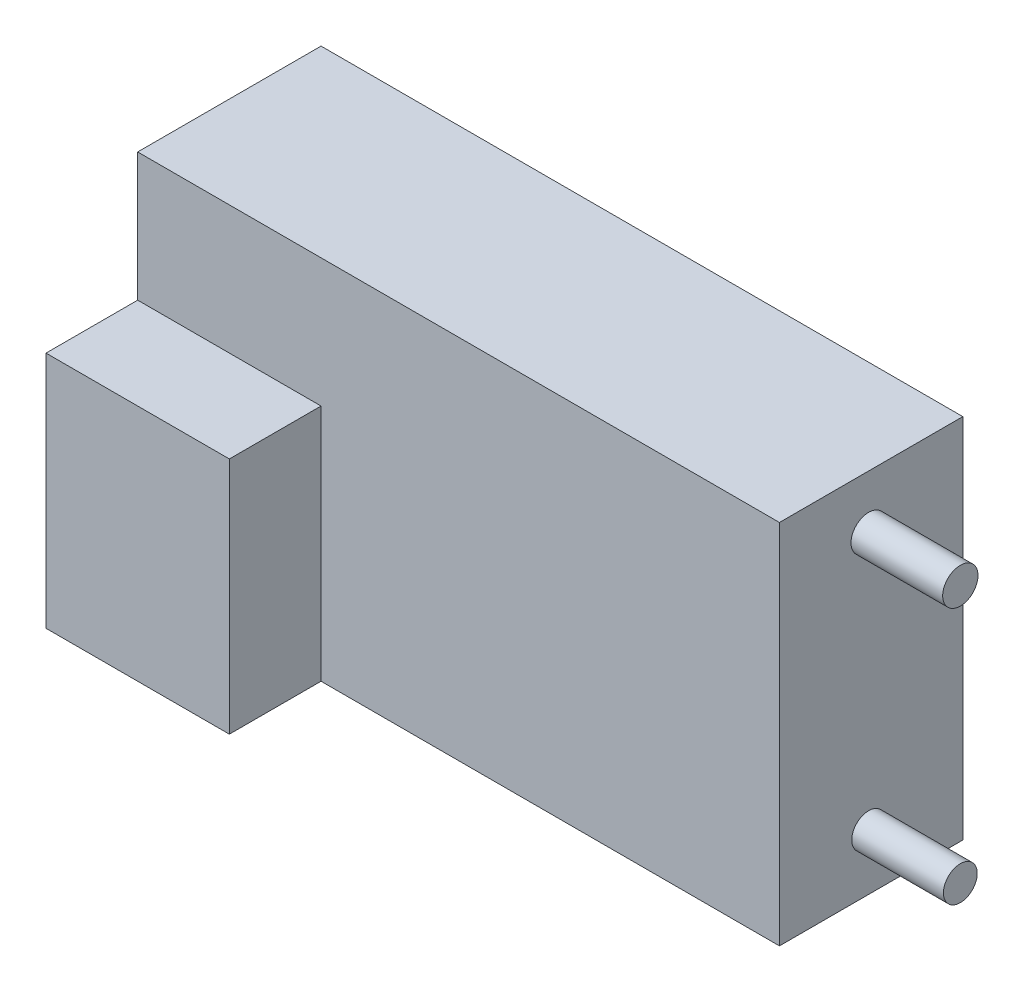
SolidWorks part; units mm, degrees
ref_plane "Plano frontal" through (0, 0, 0) normal (0, 0, 1) x (1, 0, 0)
ref_plane "Plano superior" through (0, 0, 0) normal (0, 1, 0) x (1, 0, 0)
ref_plane "Plano direito" through (0, 0, 0) normal (1, 0, 0) x (0, 0, -1)
sketch "Esboço1" plane through (0, 0, 0) normal (0, 0, 1) x (1, 0, 0)
  line L1 (-16.2743, 10.6668) -> (18.7257, 10.6668)
  line L2 (-16.2743, 10.6668) -> (-16.2743, -9.3332)
  line L3 (-16.2743, -9.3332) -> (18.7257, -9.3332)
  line L4 (18.7257, 10.6668) -> (18.7257, -9.3332)
  dimension "D1" = 35
  dimension "D2" = 20
extrude "Ressalto-extrusão1" add sketch "Esboço1" along normal blind 10
sketch "Esboço2" plane through (0, 0, 10) normal (0, 0, 1) x (1, 0, 0)
  line L1 (-16.2743, -9.3332) -> (-6.2743, -9.3332)
  line L2 (-16.2743, -9.3332) -> (-16.2743, 3.6668)
  line L3 (-16.2743, 3.6668) -> (-6.2743, 3.6668)
  line L4 (-6.2743, -9.3332) -> (-6.2743, 3.6668)
  dimension "D1" = 13
  dimension "D2" = 10
extrude "Ressalto-extrusão2" add sketch "Esboço2" along normal blind 5
sketch "Esboço3" plane through (18.7257, 0, 0) normal (1, 0, 0) x (0, 0, -1)
  circle A0 centre (-5.1351, -6.3012) radius 0.9221
  circle A1 centre (-5.1351, 7.7503) radius 0.9635
extrude "Ressalto-extrusão3" add sketch "Esboço3" along normal blind 5
